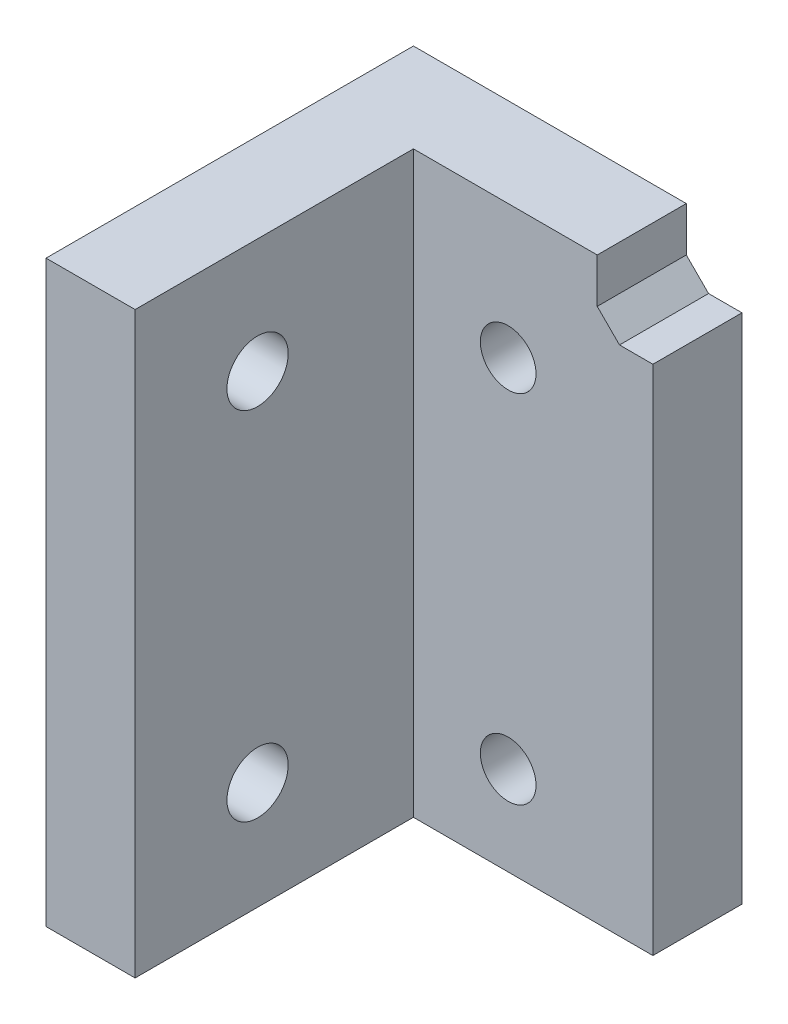
SolidWorks part; units mm, degrees
ref_plane "Plan de face" through (0, 0, 0) normal (0, 0, 1) x (1, 0, 0)
ref_plane "Plan de dessus" through (0, 0, 0) normal (0, 1, 0) x (1, 0, 0)
ref_plane "Plan de droite" through (0, 0, 0) normal (1, 0, 0) x (0, 0, -1)
sketch "Sketch1" plane through (0, 0, 0) normal (0, 0, 1) x (1, 0, 0)
  line L1 (0, 0) -> (-24.51, 0)
  line L2 (0, 0) -> (0, 148)
  line L3 (0, 148) -> (-24.51, 148)
  line L4 (-24.51, 0) -> (-24.51, 148)
  dimension "D1" = 24.51
  dimension "D2" = 148
extrude "Boss-Extrude1" add sketch "Sketch1" along normal blind 8
sketch "Sketch2" plane through (0, 0, 8) normal (0, 0, 1) x (1, 0, 0)
  line L0 (-24.51, 0) -> (0, 0) construction
  line L1 (-24.51, 148) -> (-16.51, 148)
  line L2 (-24.51, 148) -> (-24.51, 0)
  line L3 (-24.51, 0) -> (-16.51, 0)
  line L4 (-16.51, 148) -> (-16.51, 0)
  dimension "D1" = 8
extrude "Boss-Extrude2" add sketch "Sketch2" along normal blind 25
sketch "Sketch4" plane through (0, 0, 0) normal (0, 0, -1) x (-1, 0, 0)
  line L0 (0, 0) -> (0, 148) construction
  line L1 (0, 148) -> (-20.3, 148)
  line L2 (0, 148) -> (0, 111.2)
  line L3 (0, 111.2) -> (-20.3, 111.2)
  line L4 (-20.3, 148) -> (-20.3, 111.2)
  line L6 (0, 148) -> (24.51, 148) construction
  dimension "D1" = 36.8
  dimension "D2" = 20.3
extrude "Boss-Extrude3" add sketch "Sketch4" against normal up to surface (8 mm away) up to face at (-8.255, 55.5, 8)
sketch "Sketch5" plane through (0, 0, 8) normal (0, 0, 1) x (1, 0, 0)
  line L0 (20.3, 148) -> (20.3, 111.2) construction
  line L1 (20.3, 115.2) -> (-2.7, 115.2)
  line L2 (20.3, 115.2) -> (20.3, 121.2)
  line L3 (20.3, 121.2) -> (-2.7, 121.2)
  line L4 (-2.7, 115.2) -> (-2.7, 121.2)
  line L6 (20.3, 111.2) -> (0, 111.2) construction
  line L8 (20.3, 148) -> (20.3, 111.2) construction
  line L9 (20.3, 144) -> (-2.7, 144)
  line L10 (20.3, 144) -> (20.3, 138)
  line L11 (20.3, 138) -> (-2.7, 138)
  line L12 (-2.7, 144) -> (-2.7, 138)
  line L13 (20.3, 148) -> (-16.51, 148) construction
  dimension "D1" = 6
  dimension "D2" = 4
  dimension "D3" = 23
  dimension "D4" = 6
  dimension "D5" = 4
extrude "Boss-Extrude4" add sketch "Sketch5" along normal blind 25 contours L3 L4 L1 L2
sketch "Sketch6" plane through (0, 144, 0) normal (0, 1, 0) x (1, 0, 0)
  line L3 (20.3, -33) -> (20.3, -8) construction
  circle A0 centre (6.6, -20.5) radius 2
  dimension "D1" = 4
  dimension "D2" = 13.7
extrude "Cut-Extrude2" cut sketch "Sketch6" against normal up to surface (28.8 mm away) up to face at (8.8, 115.2, 20.5)
ref_plane "Plane1" through (16.3, 0, 0) normal (1, 0, 0) x (0, 0, -1)
sketch "Sketch8" plane through (16.3, 0, 0) normal (1, 0, 0) x (0, 0, -1)
  line L0 (-8, 148) -> (-28, 144)
  line L1 (-33, 144) -> (-8, 144) construction
  line L2 (-33, 0) -> (-33, 148) construction
  dimension "D1" = 5
rib "Rib1" sketch "Sketch8" sketch "Sketch8" thickness 3 extrusion direction parallel to sketch draft on no parameters "D1"=3
ref_plane "Plane2" through (0, 129.6, 0) normal (0, 1, 0) x (1, 0, 0)
mirror "Mirror1" about plane through (0, 129.6, 0) normal (0, 1, 0) of "Rib1"
ref_plane "Plane3" through (7.55, 0, 0) normal (-1, 0, 0) x (0, 0, 1)
mirror "Mirror2" about plane through (7.55, 0, 0) normal (-1, 0, 0) of "Mirror1", "Rib1"
sketch "Sketch3" plane through (0, 0, 8) normal (0, 0, 1) x (1, 0, 0)
  line L0 (0, 0) -> (0, 111.2) construction
  line L1 (0, 0) -> (0, 111.2) construction
  line L4 (-24.51, 0) -> (0, 0) construction
  circle A0 centre (-8, 8) radius 2.5
  circle A1 centre (-8, 40) radius 2.5
  circle A2 centre (-8, 100) radius 2.5
  circle A3 centre (-8, 132) radius 2.5
  dimension "D1" = 5
  dimension "D2" = 5
  dimension "D9" = 5
  dimension "D10" = 5
  dimension "D3" = 32
  dimension "D4" = 8
  dimension "D5" = 8
  dimension "D6" = 60
  dimension "D7" = 32
  dimension "D8" = 8
extrude "Cut-Extrude1" cut sketch "Sketch3" against normal blind 10
sketch "Sketch12" plane through (-24.51, 0, 0) normal (-1, 0, 0) x (0, 0, 1)
  circle A0 centre (22, 138.8) radius 2.75
  circle A1 centre (22, 106.8) radius 2.75
  circle A2 centre (22, 41.7) radius 2.75
  circle A3 centre (22, 9.7) radius 2.75
  dimension "D1" = 5.5
  dimension "D2" = 5.5
  dimension "D4" = 5.5
  dimension "D5" = 5.5
  dimension "D3" = 32
  dimension "D6" = 65.1
  dimension "D7" = 32
extrude "Cut-Extrude3" cut sketch "Sketch12" against normal up to surface (8 mm away) up to face at (-16.51, 55.5, 26.75)
sketch "Sketch13" plane through (0, 0, 0) normal (0, 0, -1) x (-1, 0, 0)
  line L1 (0, 0) -> (-5, 0)
  line L2 (0, 0) -> (0, 46)
  line L3 (0, 46) -> (-5, 46)
  line L4 (-5, 0) -> (-5, 46)
  dimension "D1" = 5
  dimension "D2" = 46
extrude "Boss-Extrude5" add sketch "Sketch13" against normal up to surface (8 mm away) up to face at (-10.5, 132, 8)
sketch "Sketch14" plane through (0, 0, 0) normal (0, 0, -1) x (-1, 0, 0)
  line L1 (0, 111.2) -> (-3, 111.2)
  line L2 (0, 111.2) -> (0, 94.2)
  line L3 (0, 94.2) -> (-3, 94.2)
  line L4 (-3, 111.2) -> (-3, 94.2)
  dimension "D1" = 3
  dimension "D2" = 17
extrude "Boss-Extrude6" add sketch "Sketch14" against normal up to surface (8 mm away) up to face at (-10.5, 132, 8)
chamfer "Chamfer1" distance 2 angle 45 3 edges at (0, 46, 4) (3, 111.2, 4) (0, 94.2, 4)
chamfer "Chamfer2" distance 6 angle 34 2 edges at (8.8, 121.2, 8) (8.8, 138, 8)
sketch "Sketch15" plane through (20.3, 0, 0) normal (1, 0, 0) x (0, 0, -1)
  line L0 (-33, 0) -> (-33, 148) construction
  line L1 (0, 148) -> (-33, 148)
  line L2 (0, 148) -> (0, 52)
  line L3 (0, 52) -> (-33, 52)
  line L4 (-33, 148) -> (-33, 52)
  dimension "D1" = 96
extrude "Cut-Extrude4" cut sketch "Sketch15" against normal blind 45
equation "\"D9@Sketch3\"=\"D1@Sketch3\""
equation "\"D10@Sketch3\"=\"D1@Sketch3\""
